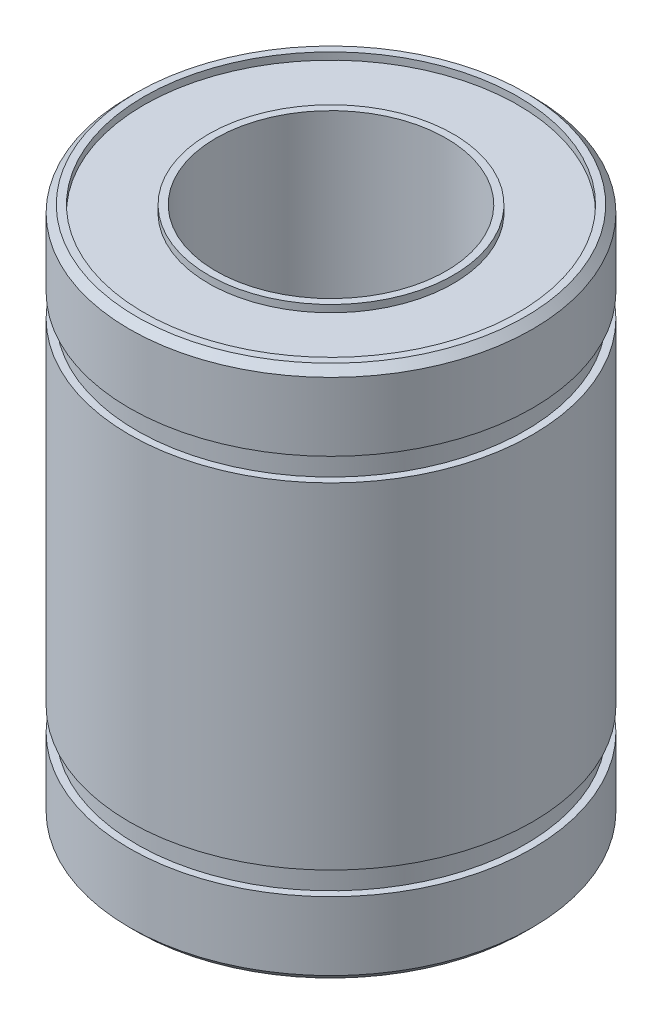
SolidWorks part; units mm, degrees
ref_plane "Front Plane" through (0, 0, 0) normal (0, 0, 1) x (1, 0, 0)
ref_plane "Top Plane" through (0, 0, 0) normal (0, 1, 0) x (1, 0, 0)
ref_plane "Right Plane" through (0, 0, 0) normal (1, 0, 0) x (0, 0, -1)
sketch "Sketch1" plane through (0, 0, 0) normal (0, 0, 1) x (1, 0, 0)
  line L0 (0, 18.5) -> (0, 0) construction
  line L1 (0, 0) -> (0, -18.5) construction
  line L2 (0, 18.5) -> (8, 18.5) construction
  line L3 (0, -18.5) -> (8, -18.5) construction
  line L4 (8, -18.5) -> (8, 18.5)
  line L5 (8, 18.5) -> (13.5, 18.5)
  line L6 (13.5, 18.5) -> (14, 18)
  line L7 (14, 18) -> (14, 13.25)
  line L8 (14, 11.65) -> (14, 13.25) construction
  line L9 (14, -13.25) -> (14, -11.65) construction
  line L10 (14, 11.65) -> (14, -11.65)
  line L11 (14, -18) -> (13.5, -18) construction
  line L12 (13.5, -18) -> (13.5, -18.5) construction
  line L13 (14, -13.25) -> (14, -18)
  line L14 (14, -18) -> (13.5, -18.5)
  line L15 (13.5, -18.5) -> (8, -18.5)
  line L16 (14, 18) -> (13.5, 18) construction
  line L17 (13.5, 18) -> (13.5, 18.5) construction
  line L18 (13.5, -18) -> (13.5, 18) construction
  line L19 (14.39, -12.45) -> (14.39, 12.45) construction
  line L20 (13.5, -12.45) -> (14.39, -12.45) construction
  line L21 (14, 13.25) -> (13.5, 13.25)
  line L22 (0, 0) -> (14, 0) construction
  line L23 (13.5, 13.25) -> (13.5, 11.65)
  line L24 (13.5, 11.65) -> (14, 11.65)
  line L25 (14, -11.65) -> (13.5, -11.65)
  line L26 (13.5, -11.65) -> (13.5, -13.25)
  line L27 (13.5, -13.25) -> (14, -13.25)
  arc A0 (14, 13.25) -> (14, 11.65) centre (14.39, 12.45) ccw construction
  arc A1 (14, -11.65) -> (14, -13.25) centre (14.39, -12.45) ccw construction
  dimension "Total_length" = 37
  dimension "Inside_diameter" = 16
  dimension "D4" = 0.5
  dimension "Distance_between_lockingrings" = 26.5
  dimension "Diameter_outside" = 28
  dimension "Locking_ring_width" = 1.6
  dimension "Locking_ring_groove_dia" = 27
revolve "Revolve1" add sketch "Sketch1" angle 360 about L0
sketch "Sketch2" plane through (0, 18.5, 0) normal (0, 1, 0) x (1, 0, 0)
  circle A0 centre (0, 0) radius 8.5
  circle A1 centre (0, 0) radius 13
  circle A2 centre (0, 0) radius 14 construction
  circle A3 centre (0, 0) radius 8 construction
  dimension "D1" = 1
  dimension "D2" = 0.5
extrude "Cut-Extrude1" cut sketch "Sketch2" against normal blind 0.5
mirror "Mirror1" about plane through (0, 0, 0) normal (0, 1, 0) of "Cut-Extrude1"
sketch "Sketch3" plane through (0, -18, 0) normal (0, -1, 0) x (1, 0, 0)
  line L0 (13, 0) -> (8.5, 0) construction
  circle A0 centre (0, 0) radius 10.35 construction
  circle A2 centre (0, 0) radius 13 construction
  circle A3 centre (0, 0) radius 8.5 construction
  text T0 "LM16UU" font "Century Gothic" height 0.8
  point P11 (10.75, 0)
  dimension "D1" = 0.4
split line "Split Line1"
